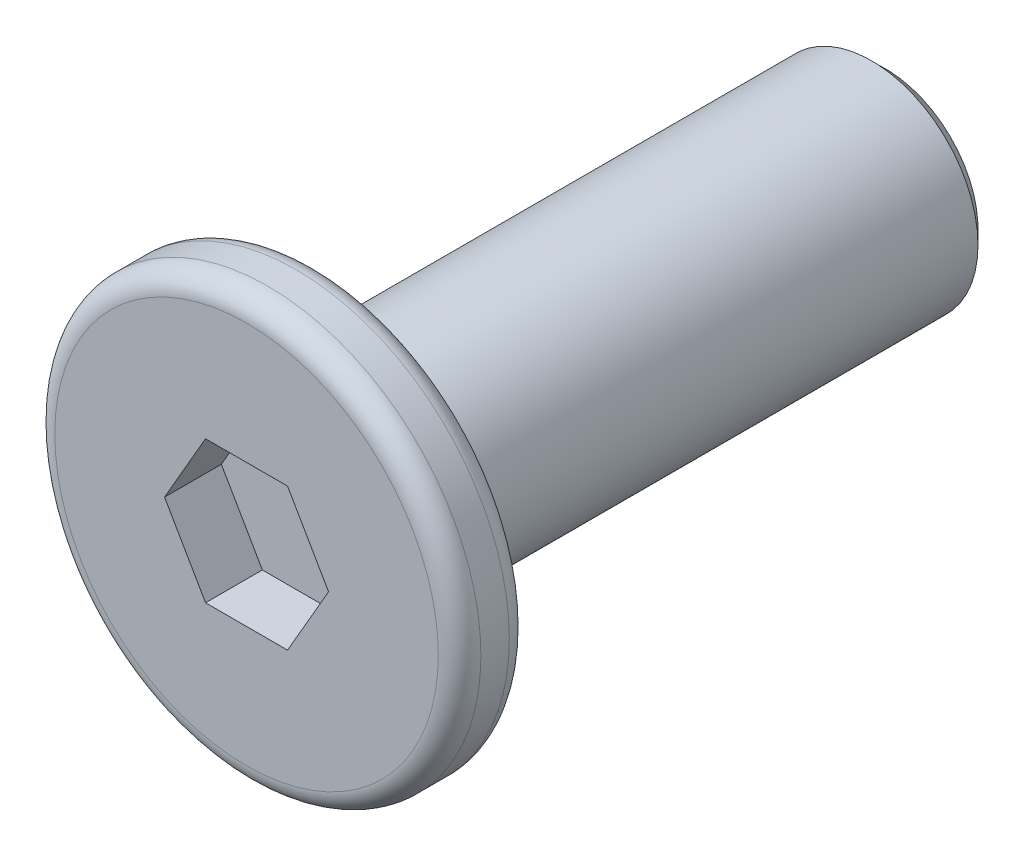
SolidWorks part; units mm, degrees
ref_plane "前视基准面" through (0, 0, 0) normal (0, 0, 1) x (1, 0, 0)
ref_plane "上视基准面" through (0, 0, 0) normal (0, 1, 0) x (1, 0, 0)
ref_plane "右视基准面" through (0, 0, 0) normal (1, 0, 0) x (0, 0, -1)
sketch "草图1" plane through (0, 0, 0) normal (0, 0, 1) x (1, 0, 0)
  circle A0 centre (0, 0) radius 3
  dimension "D1" = 6
extrude "凸台-拉伸1" add sketch "草图1" along normal mid plane 1
sketch "草图2" plane through (0, 0, -0.5) normal (0, 0, -1) x (-1, 0, 0)
  circle A0 centre (0, 0) radius 1.5
  dimension "D1" = 3
extrude "凸台-拉伸2" add sketch "草图2" along normal blind 8
chamfer "倒角1" distance 0.2 angle 45 1 edges at (-1.5, 0, -8.5)
sketch "草图3" plane through (0, 0, 0.5) normal (0, 0, 1) x (1, 0, 0)
  line L1 (1.1547, 0) -> (0.5774, 1)
  line L2 (0.5774, 1) -> (-0.5774, 1)
  line L3 (-0.5774, 1) -> (-1.1547, 0)
  line L4 (-1.1547, 0) -> (-0.5774, -1)
  line L5 (-0.5774, -1) -> (0.5774, -1)
  line L6 (0.5774, -1) -> (1.1547, 0)
  circle A0 centre (0, 0) radius 1 construction
  dimension "D1" = 2
extrude "切除-拉伸1" cut sketch "草图3" against normal blind 0.8
fillet "圆角2" radius 0.3 2 edges at (3, 0, -0.5) (3, 0, 0.5)
